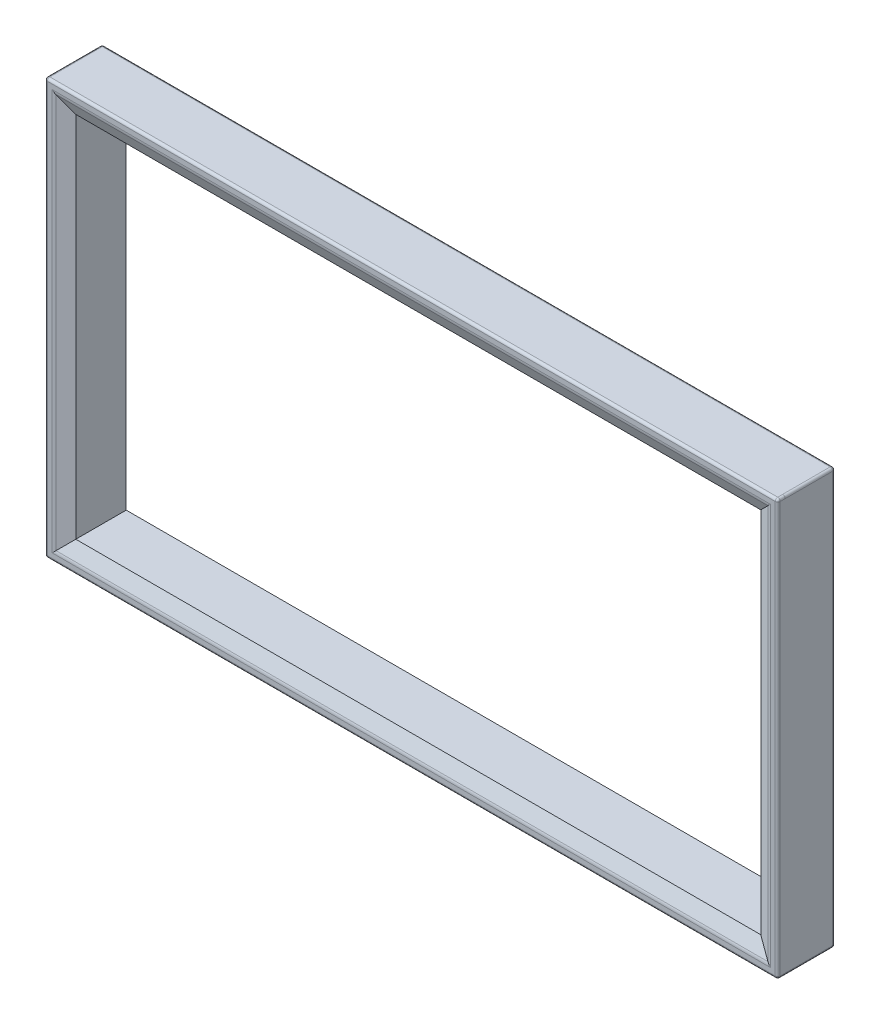
SolidWorks part; units mm, degrees
ref_plane "Płaszczyzna przednia" through (0, 0, 0) normal (0, 0, 1) x (1, 0, 0)
ref_plane "Płaszczyzna górna" through (0, 0, 0) normal (0, 1, 0) x (1, 0, 0)
ref_plane "Płaszczyzna prawa" through (0, 0, 0) normal (1, 0, 0) x (0, 0, -1)
ref_plane "Płaszczyzna1" through (0, 0, 393) normal (0, 0, 1) x (1, 0, 0)
sketch "Szkic2" plane through (0, 0, 393) normal (0, 0, 1) x (1, 0, 0)
  line L1 (-1486.2478, -785.1269) -> (1353.7522, -785.1269) construction
  line L2 (-1486.2478, -785.1269) -> (-1486.2478, 784.8731) construction
  line L3 (-1486.2478, 784.8731) -> (1353.7522, 784.8731) construction
  line L4 (1353.7522, -785.1269) -> (1353.7522, 784.8731) construction
  line L5 (-1486.2478, -785.1269) -> (1353.7522, 784.8731) construction
  line L6 (-1486.2478, 784.8731) -> (1353.7522, -785.1269) construction
  line L7 (-1438.2478, -737.1269) -> (1305.7522, -737.1269)
  line L8 (-1438.2478, -737.1269) -> (-1438.2478, 736.8731)
  line L9 (-1438.2478, 736.8731) -> (1305.7522, 736.8731)
  line L10 (1305.7522, -737.1269) -> (1305.7522, 736.8731)
  line L11 (-1438.2478, -737.1269) -> (1305.7522, 736.8731) construction
  line L12 (-1438.2478, 736.8731) -> (1305.7522, -737.1269) construction
  line L13 (-1534.2478, -833.1269) -> (1401.7522, -833.1269)
  line L14 (-1534.2478, -833.1269) -> (-1534.2478, 832.8731)
  line L15 (-1534.2478, 832.8731) -> (1401.7522, 832.8731)
  line L16 (1401.7522, -833.1269) -> (1401.7522, 832.8731)
  line L17 (-1534.2478, -833.1269) -> (1401.7522, 832.8731) construction
  line L18 (-1534.2478, 832.8731) -> (1401.7522, -833.1269) construction
  point P0 (-66.2478, -0.1269)
  point P7 (-66.2478, -0.1269)
  point P12 (-66.2478, -0.1269)
  dimension "D1" = 2840
  dimension "D2" = 48
  dimension "D3" = 48
  dimension "D4" = 48
  dimension "D5" = 48
extrude "Dodanie-wyciągnięcie1" add sketch "Szkic2" along normal blind 30
chamfer "Sfazowanie1" distance 60 angle 25 4 edges at (-1438.2478, -0.1269, 423) (-66.2478, 736.8731, 423) (1305.7522, -0.1269, 423) (-66.2478, -737.1269, 423)
fillet "Zaokrąglenie1" radius 30 4 edges at (-66.2478, 796.8731, 423) (1365.7522, -0.1269, 423) (-66.2478, -797.1269, 423) (-1498.2478, -0.1269, 423)
fillet "Zaokrąglenie2" radius 10 8 edges at (1401.7522, -833.1269, 408) (1401.7522, 832.8731, 408) (-1534.2478, 832.8731, 408) (-1534.2478, -833.1269, 408) (-66.2478, -833.1269, 423) (1401.7522, -0.1269, 423) (-66.2478, 832.8731, 423) (-1534.2478, -0.1269, 423)
sketch "Szkic3" plane through (0, 0, 393) normal (0, 0, -1) x (-1, 0, 0)
  line L0 (-1353.7522, 784.8731) -> (1486.2478, -785.1269) construction
  line L1 (-1401.7522, -833.1269) -> (1534.2478, -833.1269)
  line L2 (-1401.7522, -833.1269) -> (-1401.7522, 832.8731)
  line L3 (-1401.7522, 832.8731) -> (1534.2478, 832.8731)
  line L4 (1534.2478, -833.1269) -> (1534.2478, 832.8731)
  line L5 (-1401.7522, -833.1269) -> (1534.2478, 832.8731) construction
  line L6 (-1401.7522, 832.8731) -> (1534.2478, -833.1269) construction
  line L7 (1438.2478, -737.1269) -> (-1305.7522, -737.1269)
  line L8 (1438.2478, -737.1269) -> (1438.2478, 736.8731)
  line L9 (1438.2478, 736.8731) -> (-1305.7522, 736.8731)
  line L10 (-1305.7522, -737.1269) -> (-1305.7522, 736.8731)
  line L11 (1438.2478, -737.1269) -> (-1305.7522, 736.8731) construction
  line L12 (1438.2478, 736.8731) -> (-1305.7522, -737.1269) construction
  point P0 (66.2478, -0.1269)
  point P6 (66.2478, -0.1269)
  dimension "D1" = 1666
  dimension "D2" = 2936
extrude "Dodanie-wyciągnięcie2" add sketch "Szkic3" along normal blind 200
fillet "Zaokrąglenie3" radius 10 8 edges at (-1534.2478, -833.1269, 293) (-66.2478, -833.1269, 193) (1401.7522, -833.1269, 293) (1401.7522, -0.1269, 193) (1401.7522, 832.8731, 293) (-66.2478, 832.8731, 193) (-1534.2478, -0.1269, 193) (-1534.2478, 832.8731, 293)
sketch "Szkic4" plane through (0, 0, 193) normal (0, 0, -1) x (-1, 0, 0)
  line L0 (-1353.7522, -515.1269) -> (-1363.7522, -515.1269)
  line L1 (-1353.7522, 784.8731) -> (-1083.7522, 784.8731) construction
  line L2 (-1353.7522, 784.8731) -> (-1353.7522, 514.8731) construction
  line L3 (-1353.7522, 514.8731) -> (-1083.7522, 514.8731)
  line L4 (-1083.7522, 784.8731) -> (-1083.7522, 514.8731)
  line L5 (-33.7522, 592.3731) -> (166.2478, 592.3731)
  line L6 (-33.7522, 592.3731) -> (-33.7522, 792.3731)
  line L7 (-33.7522, 792.3731) -> (166.2478, 792.3731)
  line L8 (166.2478, 592.3731) -> (166.2478, 792.3731)
  line L9 (-33.7522, 592.3731) -> (166.2478, 792.3731) construction
  line L10 (-33.7522, 792.3731) -> (166.2478, 592.3731) construction
  line L11 (-33.7522, -792.6269) -> (166.2478, -792.6269)
  line L12 (-33.7522, -792.6269) -> (-33.7522, -592.6269)
  line L13 (-33.7522, -592.6269) -> (166.2478, -592.6269)
  line L14 (166.2478, -792.6269) -> (166.2478, -592.6269)
  line L15 (-33.7522, -792.6269) -> (166.2478, -592.6269) construction
  line L16 (-33.7522, -592.6269) -> (166.2478, -792.6269) construction
  line L17 (-1353.7522, -785.1269) -> (-1083.7522, -785.1269) construction
  line L18 (-1353.7522, -785.1269) -> (-1353.7522, -515.1269) construction
  line L19 (-1353.7522, -515.1269) -> (-1083.7522, -515.1269)
  line L20 (-1083.7522, -785.1269) -> (-1083.7522, -515.1269)
  line L21 (1486.2478, -785.1269) -> (1216.2478, -785.1269) construction
  line L22 (1486.2478, -785.1269) -> (1486.2478, -515.1269) construction
  line L23 (1486.2478, -515.1269) -> (1216.2478, -515.1269)
  line L24 (1216.2478, -785.1269) -> (1216.2478, -515.1269)
  line L25 (1486.2478, 784.8731) -> (1216.2478, 784.8731) construction
  line L26 (1486.2478, 784.8731) -> (1486.2478, 514.8731) construction
  line L27 (1486.2478, 514.8731) -> (1216.2478, 514.8731)
  line L28 (1216.2478, 784.8731) -> (1216.2478, 514.8731)
  line L29 (-1363.7522, -515.1269) -> (-1363.7522, -795.1269)
  line L30 (-1363.7522, -795.1269) -> (-1083.7522, -795.1269)
  line L31 (-1083.7522, -795.1269) -> (-1083.7522, -785.1269)
  line L32 (-1353.7522, 514.8731) -> (-1363.7522, 514.8731)
  line L33 (-1363.7522, 514.8731) -> (-1363.7522, 794.8731)
  line L34 (-1363.7522, 794.8731) -> (-1083.7522, 794.8731)
  line L35 (-1083.7522, 794.8731) -> (-1083.7522, 784.8731)
  line L36 (1216.2478, 784.8731) -> (1216.2478, 794.8731)
  line L37 (1216.2478, 794.8731) -> (1496.2478, 794.8731)
  line L38 (1496.2478, 794.8731) -> (1496.2478, 514.8731)
  line L39 (1496.2478, 514.8731) -> (1486.2478, 514.8731)
  line L40 (1486.2478, -515.1269) -> (1496.2478, -515.1269)
  line L41 (1496.2478, -515.1269) -> (1496.2478, -795.1269)
  line L42 (1496.2478, -795.1269) -> (1216.2478, -795.1269)
  line L43 (1216.2478, -795.1269) -> (1216.2478, -785.1269)
  point P5 (66.2478, 692.3731)
  point P11 (66.2478, -692.6269)
  dimension "D1" = 270
  dimension "D2" = 200
  dimension "D3" = 200
  dimension "D4" = 270
  dimension "D5" = 270
  dimension "D6" = 270
  dimension "D7" = 270
  dimension "D8" = 270
  dimension "D9" = 10
  dimension "D10" = 10
  dimension "D11" = 200
  dimension "D12" = 200
  dimension "D13" = 270
  dimension "D14" = 10
  dimension "D15" = 10
  dimension "D16" = 10
  dimension "D17" = 10
  dimension "D18" = 10
  dimension "D19" = 10
sketch "Szkic6" plane through (0, -19.6919, 42.2295) normal (0, -0.4226, 0.9063) x (1, 0, 0)
  line L0 (-1438.2478, 834.7772) -> (-1336.2478, 834.7772)
  line L1 (1305.7522, 834.7772) -> (-1438.2478, 834.7772) construction
  line L2 (1305.7522, 834.7772) -> (1203.7522, 834.7772)
  line L3 (-1336.2478, 834.7772) -> (-1018.7478, 834.7772)
  line L4 (-1018.7478, 834.7772) -> (-701.2478, 834.7772)
  line L5 (-701.2478, 834.7772) -> (-383.7478, 834.7772)
  line L6 (-383.7478, 834.7772) -> (-66.2478, 834.7772)
  line L7 (-66.2478, 834.7772) -> (251.2522, 834.7772)
  line L8 (251.2522, 834.7772) -> (568.7522, 834.7772)
  line L9 (568.7522, 834.7772) -> (886.2522, 834.7772)
  line L10 (886.2522, 834.7772) -> (1203.7522, 834.7772)
  line L11 (-1336.2478, 834.7772) -> (-1336.2478, 894.329)
  line L12 (1359.7245, 894.329) -> (-1492.2201, 894.329) construction
  line L13 (-1018.7478, 834.7772) -> (-1018.7478, 894.329)
  line L14 (-701.2478, 834.7772) -> (-701.2478, 894.329)
  line L15 (-383.7478, 834.7772) -> (-383.7478, 894.329)
  line L16 (-66.2478, 834.7772) -> (-66.2478, 894.329)
  line L17 (251.2522, 834.7772) -> (251.2522, 894.329)
  line L18 (568.7522, 834.7772) -> (568.7522, 894.329)
  line L19 (886.2522, 834.7772) -> (886.2522, 894.329)
  point P8 (886.2522, 864.5531)
  point P26 (568.7522, 864.5531)
  point P27 (251.2522, 864.5531)
  point P28 (-66.2478, 864.5531)
  point P29 (-383.7478, 864.5531)
  point P30 (-701.2478, 864.5531)
  point P31 (-1018.7478, 864.5531)
  dimension "D1" = 102
  dimension "D2" = 102
  dimension "D3" = 317.5
  dimension "D4" = 317.5
  dimension "D5" = 317.5
  dimension "D6" = 317.5
  dimension "D7" = 317.5
  dimension "D8" = 317.5
  dimension "D9" = 317.5
sketch "Szkic7" plane through (0, 19.6466, 42.1323) normal (0, 0.4226, 0.9063) x (1, 0, 0)
  line L0 (-1438.2478, -835.0071) -> (-1336.2478, -835.0071)
  line L1 (-1438.2478, -835.0071) -> (1305.7522, -835.0071) construction
  line L2 (-1336.2478, -835.0071) -> (-1018.7478, -835.0071)
  line L3 (-1018.7478, -835.0071) -> (-701.2478, -835.0071)
  line L4 (-701.2478, -835.0071) -> (-383.7478, -835.0071)
  line L5 (-383.7478, -835.0071) -> (-66.2478, -835.0071)
  line L6 (-66.2478, -835.0071) -> (251.2522, -835.0071)
  line L7 (251.2522, -835.0071) -> (568.7522, -835.0071)
  line L8 (568.7522, -835.0071) -> (886.2522, -835.0071)
  line L9 (-1336.2478, -835.0071) -> (-1336.2478, -894.559)
  line L10 (-1492.2201, -894.559) -> (1359.7245, -894.559) construction
  line L11 (-1018.7478, -835.0071) -> (-1018.7478, -894.559)
  line L12 (-701.2478, -835.0071) -> (-701.2478, -894.559)
  line L13 (-383.7478, -835.0071) -> (-383.7478, -894.559)
  line L14 (-383.7478, -835.0071) -> (-383.7478, -894.559)
  line L15 (251.2522, -835.0071) -> (251.2522, -894.559)
  line L16 (568.7522, -835.0071) -> (568.7522, -894.559)
  line L17 (886.2522, -835.0071) -> (886.2522, -894.559)
  point P9 (886.2522, -864.783)
  point P22 (568.7522, -864.783)
  point P23 (251.2522, -864.783)
  point P24 (-383.7478, -864.783)
  point P25 (-701.2478, -864.783)
  point P26 (-1018.7478, -864.783)
  dimension "D1" = 102
  dimension "D2" = 317.5
  dimension "D3" = 317.5
  dimension "D4" = 317.5
  dimension "D5" = 317.5
  dimension "D6" = 317.5
  dimension "D7" = 317.5
  dimension "D8" = 317.5
sketch "Szkic8" plane through (-105.5779, 0, -226.4126) normal (0.4226, 0, 0.9063) x (0.9063, 0, -0.4226)
  line L0 (-1470.4385, -737.1269) -> (-1470.4385, -635.1269)
  line L1 (-1470.4385, 736.8731) -> (-1470.4385, -737.1269) construction
  line L2 (-1470.4385, -635.1269) -> (-1470.4385, -317.6269)
  line L3 (-1470.4385, 634.8731) -> (-1470.4385, 736.8731)
  line L4 (-1470.4385, -317.6269) -> (-1470.4385, -0.1269)
  line L5 (-1470.4385, -0.1269) -> (-1470.4385, 317.3731)
  line L6 (-1470.4385, -635.1269) -> (-1529.9903, -635.1269)
  line L7 (-1529.9903, 790.8454) -> (-1529.9903, -791.0991) construction
  line L8 (-1470.4385, -317.6269) -> (-1529.9903, -317.6269)
  line L9 (-1470.4385, -0.1269) -> (-1529.9903, -0.1269)
  line L10 (-1470.4385, 317.3731) -> (-1529.9903, 317.3731)
  point P10 (-1500.2144, -317.6269)
  point P16 (-1500.2144, -0.1269)
  point P19 (-1500.2144, 317.3731)
  dimension "D1" = 102
  dimension "D2" = 102
  dimension "D3" = 317.5
  dimension "D4" = 317.5
  dimension "D5" = 317.5
